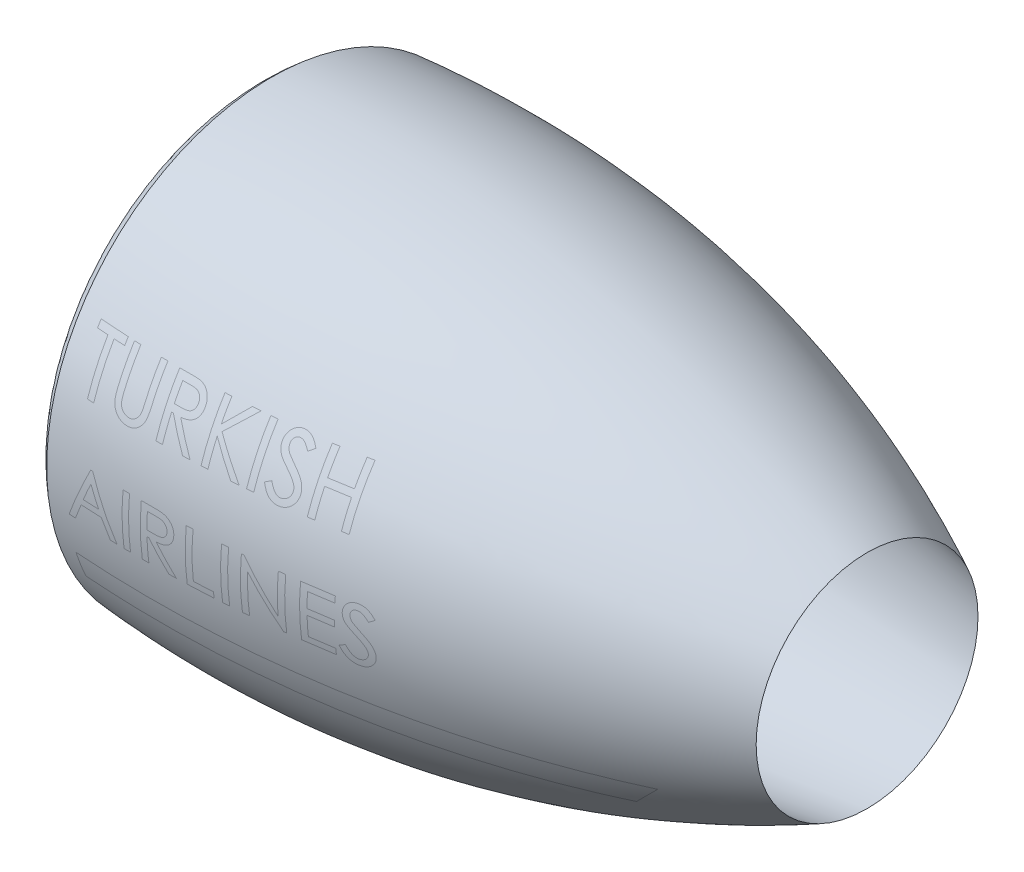
SolidWorks part; units mm, degrees
ref_plane "Ön Düzlem" through (0, 0, 0) normal (0, 0, 1) x (1, 0, 0)
ref_plane "Üst Düzlem" through (0, 0, 0) normal (0, 1, 0) x (1, 0, 0)
ref_plane "Sağ Düzlem" through (0, 0, 0) normal (1, 0, 0) x (0, 0, -1)
sketch "Sketch1" plane through (0, 0, 0) normal (0, 0, 1) x (1, 0, 0)
  line L0 (650.3583, 0) -> (0, 0) construction
  line L1 (0, 0) -> (0, 218.8109) construction
  line L2 (0, 180) -> (25, 180)
  line L3 (25, 180) -> (34.6195, 190)
  line L4 (34.6195, 190) -> (59.6195, 190)
  line L5 (580, 108) -> (59.6195, 190)
  spline S0 degree 2 poles (0, 218.8109) (307.3116, 244.484) (580, 108) knots 0 0 0 1 1 1
  spline S1 degree 2 poles (0, 218.8109) (-34.0804, 190.616) (0, 180) knots 0 0 0 1 1 1
  dimension "D1" = 580
  dimension "D2" = 108
  dimension "D3" = 180
  dimension "D4" = 190
  dimension "D5" = 25
  dimension "D6" = 25
revolve "Revolve1" add sketch "Sketch1" angle 360 about L0
ref_plane "Plane1" through (0, 0, 250) normal (0, 0, 1) x (1, 0, 0)
sketch "Sketch2" plane through (0, 0, 250) normal (0, 0, 1) x (1, 0, 0)
  line L0 (19.5953, 68.1544) -> (502.5792, 68.1544) construction
  line L1 (19.5953, -29.5157) -> (502.5792, -29.5157) construction
  line L2 (19.5953, -91.7669) -> (477.8934, -91.7669) construction
  line L3 (502.5792, -67.0811) -> (477.8934, -91.7669)
  line L4 (19.5953, -91.7669) -> (477.8934, -91.7669)
  line L5 (19.5953, -91.7669) -> (19.5953, -67.0811)
  line L6 (19.5953, -67.0811) -> (502.5792, -67.0811)
  text T0 "TURKISH" font "Century Gothic" height 50
  text T1 "AIRLINES" font "Century Gothic" height 50
split line "Split Line1"
